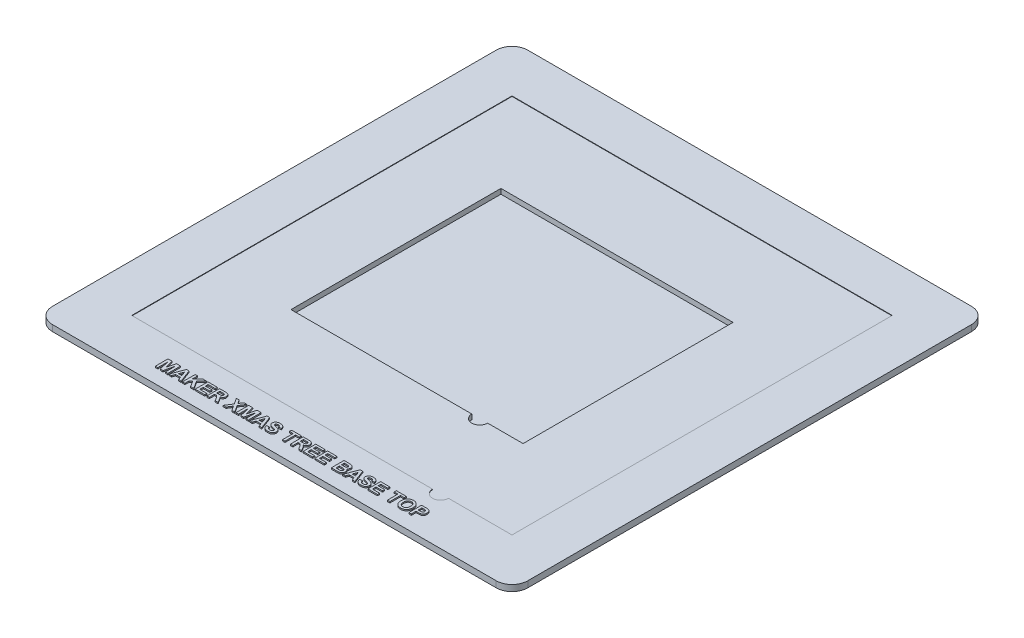
SolidWorks part; units mm, degrees
ref_plane "Front Plane" through (0, 0, 0) normal (0, 0, 1) x (1, 0, 0)
ref_plane "Top Plane" through (0, 0, 0) normal (0, 1, 0) x (1, 0, 0)
ref_plane "Right Plane" through (0, 0, 0) normal (1, 0, 0) x (0, 0, -1)
sketch "Sketch1" plane through (0, 0, 0) normal (0, 1, 0) x (1, 0, 0)
  line L1 (-70, 75) -> (70, 75)
  line L2 (-75, 70) -> (-75, -70)
  line L3 (-70, -75) -> (70, -75)
  line L4 (75, 70) -> (75, -70)
  line L5 (-75, 75) -> (75, -75) construction
  line L6 (-75, -75) -> (75, 75) construction
  arc A0 (-75, -70) -> (-70, -75) centre (-70, -70) ccw
  arc A1 (75, -70) -> (70, -75) centre (70, -70) cw
  arc A2 (75, 70) -> (70, 75) centre (70, 70) ccw
  arc A3 (-75, 70) -> (-70, 75) centre (-70, 70) cw
  point P0 (0, 0)
  dimension "D3" = 5
  dimension "D1" = 150
  dimension "D2" = 150
extrude "Boss-Extrude1" add sketch "Sketch1" along normal blind 1.95
sketch "Sketch2" plane through (0, 1.95, 0) normal (0, 1, 0) x (1, 0, 0)
  line L0 (39.9479, -60) -> (60, -60)
  line L1 (-60, 60) -> (60, 60)
  line L2 (-60, 60) -> (-60, -60)
  line L3 (-60, -60) -> (34.9479, -60)
  line L4 (60, 60) -> (60, -60)
  line L5 (-60, 60) -> (60, -60) construction
  line L6 (-60, -60) -> (60, 60) construction
  arc A0 (34.9479, -60) -> (39.9479, -60) centre (37.4479, -60) ccw
  point P0 (0, 0)
  dimension "D4" = 2.5
  dimension "D1" = 120
  dimension "D2" = 120
  dimension "D3" = 5
extrude "Cut-Extrude1" cut sketch "Sketch2" against normal blind 0.15
sketch "Sketch3" plane through (0, 1.8, 0) normal (0, 1, 0) x (1, 0, 0)
  line L0 (25.4482, -33.125) -> (36.625, -33.125)
  line L1 (-36.625, 33.125) -> (36.625, 33.125)
  line L2 (-36.625, 33.125) -> (-36.625, -33.125)
  line L3 (-36.625, -33.125) -> (20.4482, -33.125)
  line L4 (36.625, 33.125) -> (36.625, -33.125)
  line L5 (-36.625, 33.125) -> (36.625, -33.125) construction
  line L6 (-36.625, -33.125) -> (36.625, 33.125) construction
  arc A0 (20.4482, -33.125) -> (25.4482, -33.125) centre (22.9482, -33.125) ccw
  point P0 (0, 0)
  dimension "D4" = 2.5
  dimension "D1" = 73.25
  dimension "D2" = 66.25
  dimension "D3" = 5
extrude "Cut-Extrude2" cut sketch "Sketch3" against normal blind 1.6
sketch "Sketch5" plane through (0, 1.95, 0) normal (0, 1, 0) x (1, 0, 0)
  text T0 "<b>MAKER XMAS TREE BASE TOP</b>" font "Arial" height 4
extrude "Boss-Extrude2" add sketch "Sketch5" along normal blind 0.4
